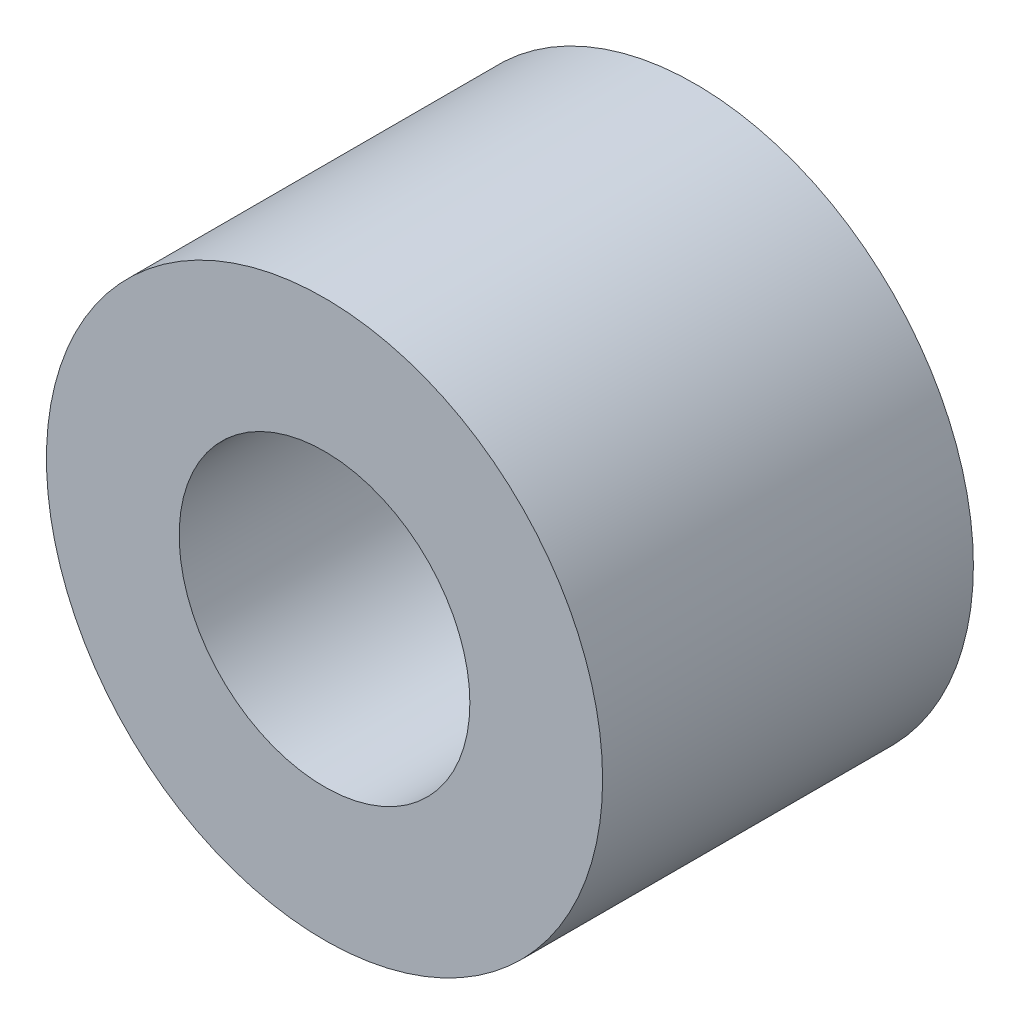
SolidWorks part; units mm, degrees
material "6061-T6 (SS)"
ref_plane "Front Plane" through (0, 0, 0) normal (0, 0, 1) x (1, 0, 0)
ref_plane "Top Plane" through (0, 0, 0) normal (0, 1, 0) x (1, 0, 0)
ref_plane "Right Plane" through (0, 0, 0) normal (1, 0, 0) x (0, 0, -1)
sketch "Sketch1" plane through (0, 0, 0) normal (0, 0, 1) x (1, 0, 0)
  circle A0 centre (0, 0) radius 2.4892
  circle A1 centre (0, 0) radius 4.7625
  dimension "D1" = 4.9784
  dimension "D2" = 9.525
extrude "Boss-Extrude1" add sketch "Sketch1" along normal mid plane 6.35
